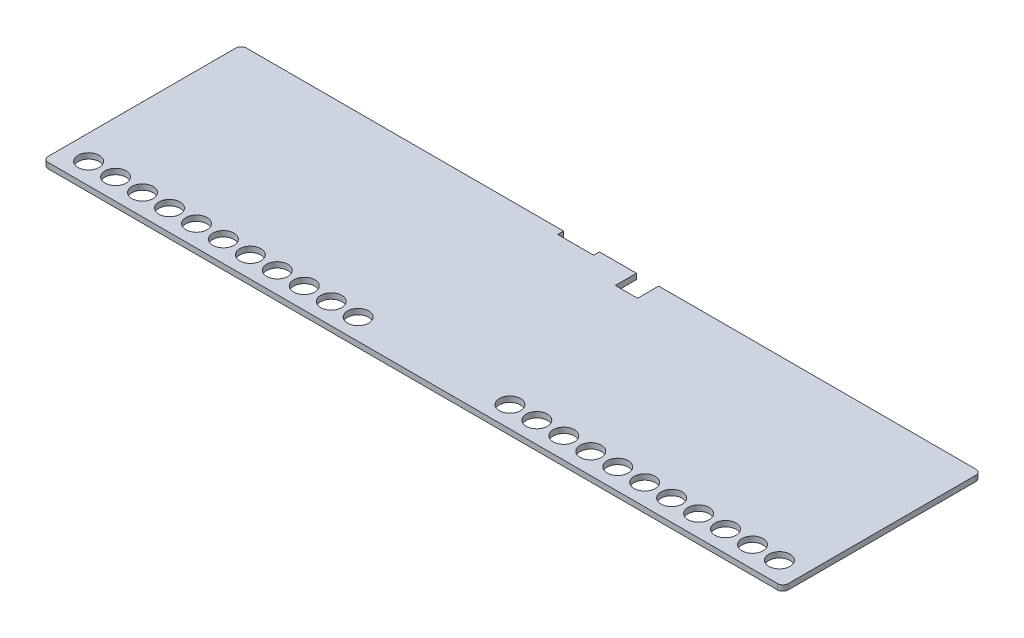
SolidWorks part; units mm, degrees
material "Custom FR4"
ref_plane "Front Plane" through (0, 0, 0) normal (0, 0, 1) x (1, 0, 0)
ref_plane "Top Plane" through (0, 0, 0) normal (0, 1, 0) x (1, 0, 0)
ref_plane "Right Plane" through (0, 0, 0) normal (1, 0, 0) x (0, 0, -1)
sketch "Sketch1" plane through (0, 0, 0) normal (0, 1, 0) x (1, 0, 0)
  line L0 (-69, 17.75) -> (69, -17.75) construction
  line L1 (-69, 18.75) -> (-9, 18.75)
  line L2 (-70, 17.75) -> (-70, -17.75)
  line L3 (-69, -18.75) -> (69, -18.75)
  line L4 (70, 17.75) -> (70, -17.75)
  line L5 (-65.35, -14.75) -> (-65.35, -18.75) construction
  line L6 (-65.35, -14.75) -> (-70, -14.75) construction
  line L7 (70, -14.75) -> (65.35, -14.75) construction
  line L8 (65.35, -14.75) -> (65.35, -18.75) construction
  line L9 (70, 17.75) -> (69, 17.75) construction
  line L10 (69, 17.75) -> (69, 18.75) construction
  line L11 (69, -18.75) -> (69, -17.75) construction
  line L12 (69, -17.75) -> (70, -17.75) construction
  line L13 (-69, 18.75) -> (-69, 17.75) construction
  line L14 (-69, 17.75) -> (-70, 17.75) construction
  line L15 (-69, -18.75) -> (-69, -17.75) construction
  line L16 (-69, -17.75) -> (-70, -17.75) construction
  line L17 (70, 14.75) -> (9, 14.75) construction
  line L18 (9, 18.75) -> (9, 14.75)
  line L19 (9, 14.75) -> (4.8, 14.75)
  line L20 (4.8, 14.75) -> (4.8, 18.75)
  line L21 (-70, 17.65) -> (-9, 17.65) construction
  line L22 (-9, 17.65) -> (-9, 18.75)
  line L23 (-9, 17.65) -> (-2.2, 17.65)
  line L24 (-2.2, 17.65) -> (-2.2, 18.75)
  line L25 (-2.2, 17.65) -> (4.8, 17.529) construction
  line L26 (-2.2, 18.75) -> (4.8, 18.75)
  line L27 (9, 18.75) -> (69, 18.75)
  circle A0 centre (-65.35, -14.75) radius 2.0025
  circle A1 centre (-60.25, -14.75) radius 2.0025
  circle A2 centre (-55.15, -14.75) radius 2.0025
  circle A3 centre (-50.05, -14.75) radius 2.0025
  circle A4 centre (-44.95, -14.75) radius 2.0025
  circle A5 centre (-39.85, -14.75) radius 2.0025
  circle A6 centre (-34.75, -14.75) radius 2.0025
  circle A7 centre (-29.65, -14.75) radius 2.0025
  circle A8 centre (-24.55, -14.75) radius 2.0025
  circle A9 centre (-19.45, -14.75) radius 2.0025
  circle A10 centre (-14.35, -14.75) radius 2.0025
  circle A11 centre (65.35, -14.75) radius 2.0025
  circle A12 centre (60.25, -14.75) radius 2.0025
  circle A13 centre (55.15, -14.75) radius 2.0025
  circle A14 centre (50.05, -14.75) radius 2.0025
  circle A15 centre (44.95, -14.75) radius 2.0025
  circle A16 centre (39.85, -14.75) radius 2.0025
  circle A17 centre (34.75, -14.75) radius 2.0025
  circle A18 centre (29.65, -14.75) radius 2.0025
  circle A19 centre (24.55, -14.75) radius 2.0025
  circle A20 centre (19.45, -14.75) radius 2.0025
  circle A21 centre (14.35, -14.75) radius 2.0025
  arc A22 (70, 17.75) -> (69, 18.75) centre (69, 17.75) ccw
  arc A23 (69, -18.75) -> (70, -17.75) centre (69, -17.75) ccw
  arc A24 (-69, 18.75) -> (-70, 17.75) centre (-69, 17.75) ccw
  arc A25 (-70, -17.75) -> (-69, -18.75) centre (-69, -17.75) ccw
  dimension "D3" = 4.005
  dimension "D6" = 11
  dimension "D9" = 4.005
  dimension "D17" = 1
  dimension "D2" = 140
  dimension "D4" = 4
  dimension "D5" = 4.65
  dimension "D7" = 4.65
  dimension "D8" = 4
  dimension "D11" = 1
  dimension "D12" = 1
  dimension "D13" = 1
  dimension "D14" = 1
  dimension "D15" = 1
  dimension "D16" = 1
  dimension "D18" = 1
  dimension "D19" = 37.5
  dimension "D20" = 61
  dimension "D21" = 4
  dimension "D22" = 4.2
  dimension "D23" = 61
  dimension "D24" = 1.1
  dimension "D25" = 6.8
  dimension "D10" = 11
extrude "Boss-Extrude1" add sketch "Sketch1" against normal blind 1.05 contours L2 A25 L3 A23 L4 A22 L27 L18 L19 L20 L26 L24 L23 L22 L1 A24 A0 A1 A2 A3 A4 A5 A6 A7 A8 A9 A10 A11 A12 A13 A14 A15 A16
sketch "Sketch3" plane through (0, -1.05, 0) normal (0, -1, 0) x (1, 0, 0)
  line L0 (70, -17.75) -> (70, 17.75) construction
  line L1 (64.73, -1.255) -> (59.725, 2.75) construction
  line L2 (64.73, -1.255) -> (59.725, -1.255)
  line L3 (64.73, -1.255) -> (64.73, 2.75)
  line L4 (64.73, 2.75) -> (59.725, 2.75)
  line L5 (59.725, -1.255) -> (59.725, 2.75)
  line L6 (64.73, 2.75) -> (59.725, -1.255) construction
  line L7 (46.95, -1.255) -> (41.945, -1.255)
  line L8 (46.95, -1.255) -> (46.95, 2.75)
  line L9 (46.95, 2.75) -> (41.945, 2.75)
  line L10 (41.945, -1.255) -> (41.945, 2.75)
  line L11 (46.95, -1.255) -> (41.945, 2.75) construction
  line L12 (46.95, 2.75) -> (41.945, -1.255) construction
  line L13 (29.17, -1.255) -> (24.165, -1.255)
  line L14 (29.17, -1.255) -> (29.17, 2.75)
  line L15 (29.17, 2.75) -> (24.165, 2.75)
  line L16 (24.165, -1.255) -> (24.165, 2.75)
  line L17 (29.17, -1.255) -> (24.165, 2.75) construction
  line L18 (29.17, 2.75) -> (24.165, -1.255) construction
  line L19 (11.39, -1.255) -> (6.385, -1.255)
  line L20 (11.39, -1.255) -> (11.39, 2.75)
  line L21 (11.39, 2.75) -> (6.385, 2.75)
  line L22 (6.385, -1.255) -> (6.385, 2.75)
  line L23 (11.39, -1.255) -> (6.385, 2.75) construction
  line L24 (11.39, 2.75) -> (6.385, -1.255) construction
  line L25 (-6.39, -1.255) -> (-11.395, -1.255)
  line L26 (-6.39, -1.255) -> (-6.39, 2.75)
  line L27 (-6.39, 2.75) -> (-11.395, 2.75)
  line L28 (-11.395, -1.255) -> (-11.395, 2.75)
  line L29 (-6.39, -1.255) -> (-11.395, 2.75) construction
  line L30 (-6.39, 2.75) -> (-11.395, -1.255) construction
  line L31 (-24.17, -1.255) -> (-29.175, -1.255)
  line L32 (-24.17, -1.255) -> (-24.17, 2.75)
  line L33 (-24.17, 2.75) -> (-29.175, 2.75)
  line L34 (-29.175, -1.255) -> (-29.175, 2.75)
  line L35 (-24.17, -1.255) -> (-29.175, 2.75) construction
  line L36 (-24.17, 2.75) -> (-29.175, -1.255) construction
  line L37 (-41.95, -1.255) -> (-46.955, -1.255)
  line L38 (-41.95, -1.255) -> (-41.95, 2.75)
  line L39 (-41.95, 2.75) -> (-46.955, 2.75)
  line L40 (-46.955, -1.255) -> (-46.955, 2.75)
  line L41 (-41.95, -1.255) -> (-46.955, 2.75) construction
  line L42 (-41.95, 2.75) -> (-46.955, -1.255) construction
  line L43 (-59.73, -1.255) -> (-64.735, -1.255)
  line L44 (-59.73, -1.255) -> (-59.73, 2.75)
  line L45 (-59.73, 2.75) -> (-64.735, 2.75)
  line L46 (-64.735, -1.255) -> (-64.735, 2.75)
  line L47 (-59.73, -1.255) -> (-64.735, 2.75) construction
  line L48 (-59.73, 2.75) -> (-64.735, -1.255) construction
  line L49 (62.2275, 0.7475) -> (44.4475, 0.7475) construction
  line L51 (-69, 18.75) -> (69, 18.75) construction
  circle A0 centre (62.23, -8.1425) radius 1.5025
  circle A1 centre (44.45, -8.1425) radius 1.5025
  circle A2 centre (26.67, -8.1425) radius 1.5025
  circle A3 centre (8.89, -8.1425) radius 1.5025
  circle A4 centre (-8.89, -8.1425) radius 1.5025
  circle A5 centre (-26.67, -8.1425) radius 1.5025
  circle A6 centre (-44.45, -8.1425) radius 1.5025
  circle A7 centre (-62.23, -8.1425) radius 1.5025
  point P8 (62.2275, 0.7475)
  point P17 (44.4475, 0.7475)
  point P24 (26.6675, 0.7475)
  point P31 (8.8875, 0.7475)
  point P38 (-8.8925, 0.7475)
  point P45 (-26.6725, 0.7475)
  point P52 (-44.4525, 0.7475)
  point P59 (-62.2325, 0.7475)
  dimension "D4" = 3.005
  dimension "D1" = 7.77
  dimension "D2" = 5.27
  dimension "D3" = 5.005
  dimension "D5" = 8.89
  dimension "D6" = 4.005
  dimension "D8" = 17.78
  dimension "D9" = 16
  dimension "D7" = 8
extrude "Cut-Extrude8" cut sketch "Sketch3" against normal blind 0.85
